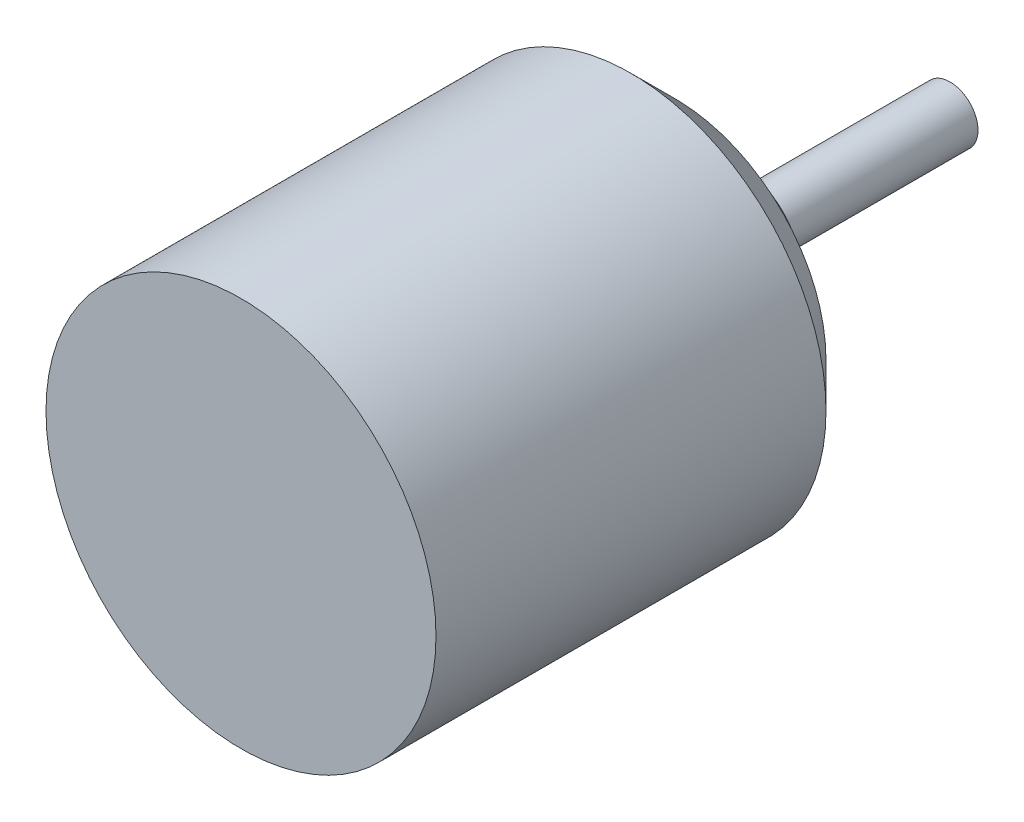
SolidWorks part; units mm, degrees
ref_plane "Front Plane" through (0, 0, 0) normal (0, 0, 1) x (1, 0, 0)
ref_plane "Top Plane" through (0, 0, 0) normal (0, 1, 0) x (1, 0, 0)
ref_plane "Right Plane" through (0, 0, 0) normal (1, 0, 0) x (0, 0, -1)
sketch "Sketch1" plane through (0, 0, 0) normal (1, 0, 0) x (0, 0, -1)
  line L0 (-48.7326, 0) -> (97.4652, 0) construction
  line L1 (0, 0) -> (0, 13.97)
  line L2 (0, 13.97) -> (27.94, 13.97)
  line L3 (31.115, 10.795) -> (31.115, 4.572)
  line L5 (50.8, 2) -> (50.8, 0)
  line L6 (50.8, 0) -> (0, 0)
  line L7 (31.115, 4.572) -> (35.56, 4.572)
  line L8 (35.56, 4.572) -> (35.56, 2)
  line L9 (35.56, 2) -> (50.8, 2)
  line L10 (27.94, 13.97) -> (31.115, 10.795)
  point P5 (31.115, 13.97)
  point P12 (0, 0)
  point P13 (0, 0)
  dimension "D1" = 4
  dimension "D2" = 27.94
  dimension "D3" = 31.115
  dimension "D4" = 50.8
  dimension "D5" = 9.144
  dimension "D6" = 35.56
revolve "Revolve1" add sketch "Sketch1" angle 360 about L0
